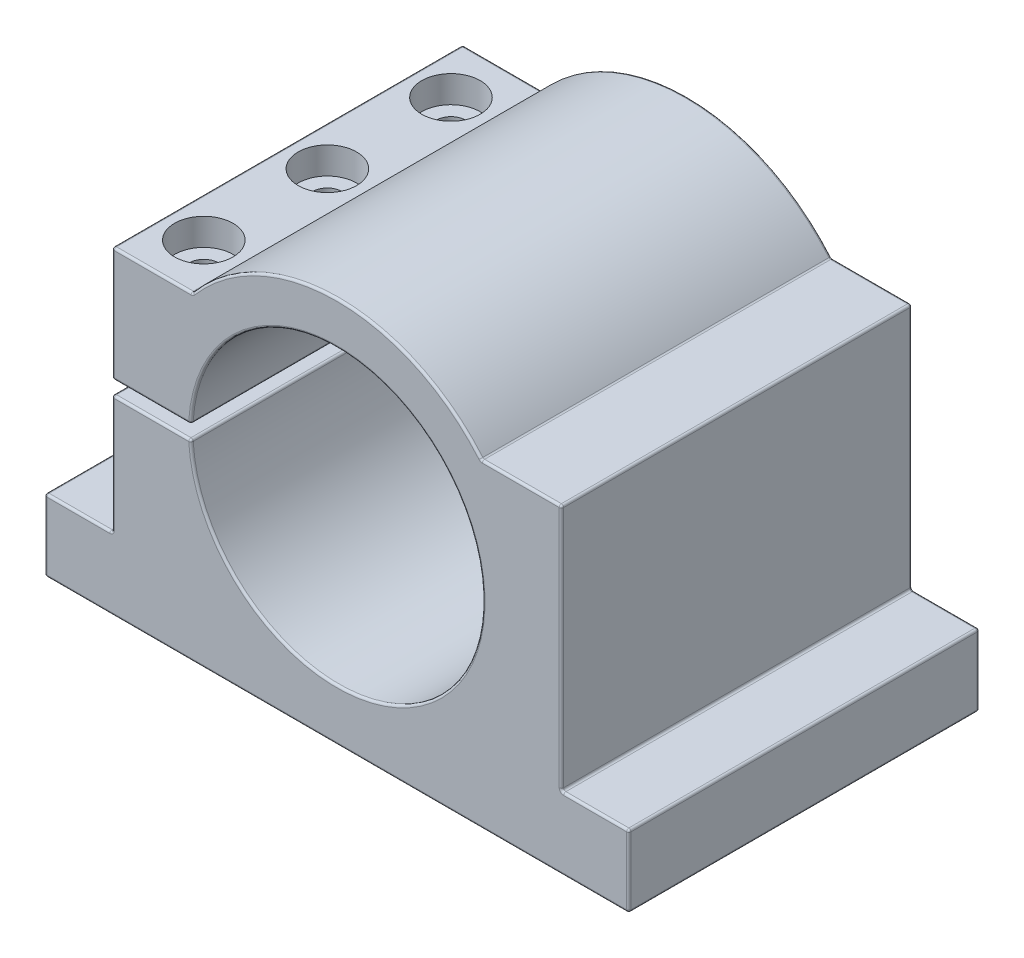
SolidWorks part; units mm, degrees
ref_plane "Спереди" through (0, 0, 0) normal (0, 0, 1) x (1, 0, 0)
ref_plane "Сверху" through (0, 0, 0) normal (0, 1, 0) x (1, 0, 0)
ref_plane "Справа" through (0, 0, 0) normal (1, 0, 0) x (0, 0, -1)
sketch "Эскиз1" plane through (0, 0, 0) normal (0, 0, 1) x (1, 0, 0)
  line L0 (0, 0) -> (0, -44) construction
  line L1 (65, -44) -> (-65, -44)
  line L2 (-65, -44) -> (-65, -28)
  line L3 (-65, -28) -> (-50, -28)
  line L4 (-50, -28) -> (-50, 27)
  line L5 (-50, 27) -> (-32.1714, 27)
  line L6 (50, 27) -> (32.1714, 27)
  line L7 (0, 1.5) -> (-50, 1.5)
  line L8 (0, 1.5) -> (0, -1.5)
  line L9 (0, -1.5) -> (-50, -1.5)
  line L10 (-50, 1.5) -> (-50, -1.5)
  line L11 (50, -28) -> (50, 27)
  line L12 (65, -28) -> (50, -28)
  line L13 (65, -44) -> (65, -28)
  circle A0 centre (0, 0) radius 32.5
  circle A1 centre (0, 0) radius 42
  point P11 (0, 42)
  dimension "D1" = 65
  dimension "D2" = 16
  dimension "D3" = 130
  dimension "D4" = 15
  dimension "D5" = 71
  dimension "D6" = 44
  dimension "D7" = 86
  dimension "D8" = 3
extrude "Бобышка-Вытянуть1" add sketch "Эскиз1" along normal mid plane 78 contours L0 A1 L9 L4 L3 L2 L1 | A1 L5 L4 L7 | A0 L0 A1 L7 | L0 A0 L9 A1 | A1 L0 L1 L13 L12 L11 L6
sketch "Эскиз2" plane through (0, 27, 0) normal (0, 1, 0) x (1, 0, 0)
  line L0 (-41.0857, 39) -> (-41.0857, -39) construction
  line L1 (-50, 39) -> (-32.1714, 39) construction
  line L2 (-50, -39) -> (-32.1714, -39) construction
  circle A0 centre (-41.0857, 27.5) radius 6.5
  circle A1 centre (-41.0857, 0) radius 6.5
  circle A2 centre (-41.0857, -27.5) radius 6.5
  dimension "D1" = 13
  dimension "D2" = 13
  dimension "D3" = 13
  dimension "D4" = 27.5
  dimension "D5" = 27.5
extrude "Вырез-Вытянуть1" cut sketch "Эскиз2" against normal blind 6
sketch "Эскиз3" plane through (0, 21, 0) normal (0, 1, 0) x (1, 0, 0)
  circle A0 centre (-41.0857, 27.5) radius 3.25
  circle A1 centre (-41.0857, 0) radius 3.25
  circle A2 centre (-41.0857, -27.5) radius 3.25
  dimension "D1" = 6.5
extrude "Вырез-Вытянуть2" cut sketch "Эскиз3" against normal up to surface (22.5 mm away) up to face at (-41.2327, -1.5, 0)
sketch "Эскиз4" plane through (0, -1.5, 0) normal (0, 1, 0) x (1, 0, 0)
  circle A0 centre (-41.0857, 27.5) radius 2.1
  circle A1 centre (-41.0857, 0) radius 2.1
  circle A2 centre (-41.0857, -27.5) radius 2.1
  dimension "D1" = 4.2
extrude "Вырез-Вытянуть3" cut sketch "Эскиз4" against normal blind 30
fillet "Скругление1" radius 0.5 42 edges at (-32.4654, 1.5, 0) (-32.4654, -1.5, 0) (-41.0857, 27, -39) (-41.0857, 27, 39) (-41.2327, 1.5, -39) (-41.2327, 1.5, 39) (32.5, 0, -39) (32.5, 0, 39) (-41.2327, -1.5, -39) (-41.2327, -1.5, 39) (-57.5, -28, -39) (-57.5, -28, 39) (0, -44, -39) (0, -44, 39) (57.5, -28, -39) (57.5, -28, 39) (41.0857, 27, -39) (41.0857, 27, 39) (65, -44, 0) (65, -28, 0) (65, -36, -39) (65, -36, 39) (50, -28, 0) (50, 27, 0) (50, -0.5, -39) (50, -0.5, 39) (32.1714, 27, 0) (-32.1714, 27, 0) (0, 42, -39) (0, 42, 39) (-65, -28, 0) (-65, -36, -39) (-65, -36, 39) (-65, -44, 0) (-50, -1.5, 0) (-50, -14.75, -39) (-50, -14.75, 39) (-50, -28, 0) (-50, 27, 0) (-50, 14.25, -39) (-50, 14.25, 39) (-50, 1.5, 0)
